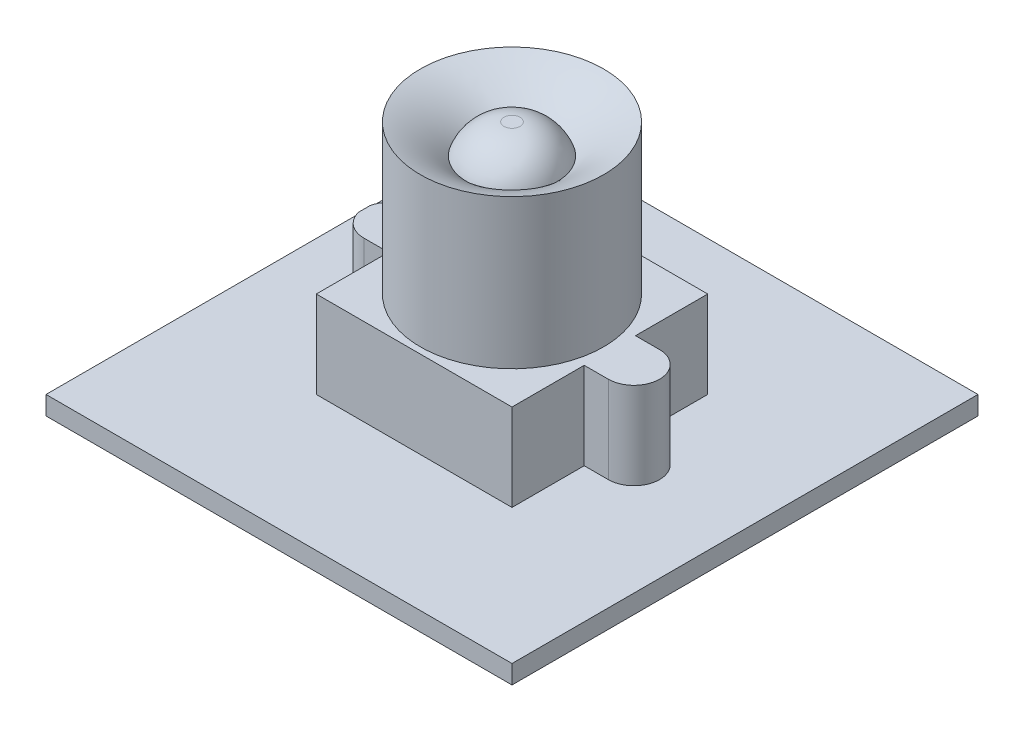
SolidWorks part; units mm, degrees
ref_plane "Front Plane" through (0, 0, 0) normal (0, 0, 1) x (1, 0, 0)
ref_plane "Top Plane" through (0, 0, 0) normal (0, 1, 0) x (1, 0, 0)
ref_plane "Right Plane" through (0, 0, 0) normal (1, 0, 0) x (0, 0, -1)
sketch "Sketch3" plane through (0, 0, 0) normal (0, 1, 0) x (1, 0, 0)
  line L1 (-19.05, 19.05) -> (19.05, 19.05)
  line L2 (-19.05, 19.05) -> (-19.05, -19.05)
  line L3 (-19.05, -19.05) -> (19.05, -19.05)
  line L4 (19.05, 19.05) -> (19.05, -19.05)
  line L5 (-19.05, 19.05) -> (19.05, -19.05) construction
  line L6 (-19.05, -19.05) -> (19.05, 19.05) construction
  point P0 (0, 0)
extrude "Boss-Extrude2" add sketch "Sketch3" along normal blind 1.524
sketch "Sketch4" plane through (0, 1.524, 0) normal (0, 1, 0) x (1, 0, 0)
  line L1 (-8.001, 8.001) -> (8.001, 8.001)
  line L2 (-8.001, 8.001) -> (-8.001, -8.001)
  line L3 (-8.001, -8.001) -> (8.001, -8.001)
  line L4 (8.001, 8.001) -> (8.001, -8.001)
  line L5 (-8.001, 8.001) -> (8.001, -8.001) construction
  line L6 (-8.001, -8.001) -> (8.001, 8.001) construction
  point P0 (0, 0)
extrude "Boss-Extrude3" add sketch "Sketch4" along normal blind 7.112
sketch "Sketch5" plane through (0, 8.636, 0) normal (0, 1, 0) x (1, 0, 0)
  circle A0 centre (0, 0) radius 7.493
extrude "Boss-Extrude4" add sketch "Sketch5" along normal blind 12.192
sketch "Sketch6" plane through (0, 8.636, 0) normal (0, 1, 0) x (1, 0, 0)
  line L1 (12.065, -2.0955) -> (-12.065, -2.0955)
  line L2 (12.065, -2.0955) -> (12.065, 2.0955)
  line L3 (12.065, 2.0955) -> (-12.065, 2.0955)
  line L4 (-12.065, -2.0955) -> (-12.065, 2.0955)
  line L5 (12.065, -2.0955) -> (-12.065, 2.0955) construction
  line L6 (12.065, 2.0955) -> (-12.065, -2.0955) construction
  circle A0 centre (9.9695, 0) radius 2.0955
  circle A2 centre (-10.0225, 0) radius 2.0955
  point P0 (0, 0)
  circle M3 centre (0, 0) radius 7.493
  line M4 (8.001, -8.001) -> (8.001, 8.001)
  line M6 (-8.001, 8.001) -> (-8.001, -8.001)
extrude "Boss-Extrude6" add sketch "Sketch6" against normal up to surface (7.112 mm away) contours A0 M4 | A0 L1 M4 | A0 L3 L1 M4 M3 | A0 L3 M4 | L3 L1 M3 | A2 L1 L3 M6 M3 | A2 L4 M6 | A2 L1 M6 | A2 M6 | A2 L3 M6 up to face at (0, 1.524, 0)
sketch "Sketch7" plane through (0, 0, 0) normal (0, 0, 1) x (1, 0, 0)
  line L0 (0, 0) -> (0, 22.3456) construction
sketch "Sketch8" plane through (0, 0, 0) normal (0, 0, 1) x (1, 0, 0)
  line L1 (7.493, 20.828) -> (-7.493, 20.828) construction
  arc A0 (-3.6833, 18.4272) -> (-0.0561, 20.828) centre (-0.3551, 17.3392) cw
  arc A1 (-3.6833, 18.4272) -> (-7.493, 20.828) centre (-10.957, 11.1082) ccw
  arc A2 (-7.493, 20.828) -> (-0.0561, 20.828) centre (-3.7746, 8.8516) cw
revolve "Cut-Revolve2" cut sketch "Sketch8" angle 360 about L0
